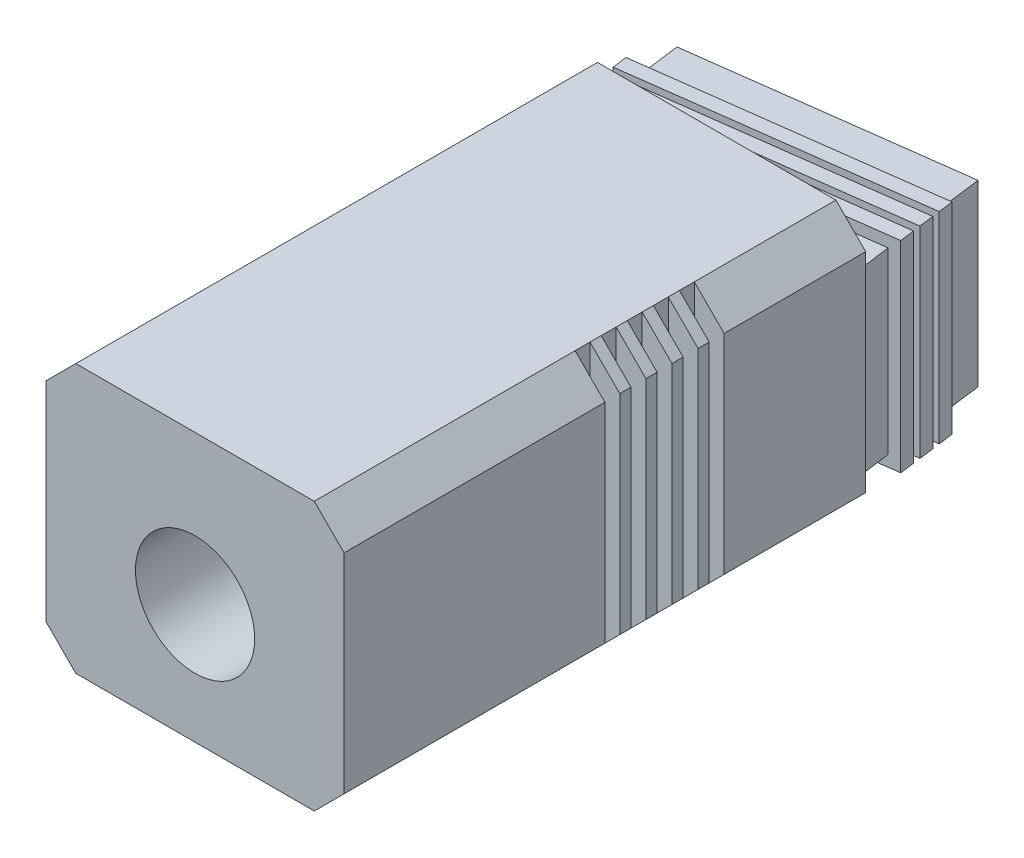
SolidWorks part; units mm, degrees
ref_plane "Front Plane" through (0, 0, 0) normal (0, 0, 1) x (1, 0, 0)
ref_plane "Top Plane" through (0, 0, 0) normal (0, 1, 0) x (1, 0, 0)
ref_plane "Right Plane" through (0, 0, 0) normal (1, 0, 0) x (0, 0, -1)
sketch "Sketch1" plane through (0, 0, 0) normal (0, 0, 1) x (1, 0, 0)
  line L0 (-10, 9) -> (-10, -9)
  line L1 (-10, 9) -> (10, 9)
  line L2 (-10, -9) -> (10, -9)
  line L3 (10, 9) -> (10, -9)
  line L4 (-10, 9) -> (10, -9) construction
  dimension "D1" = 20
  dimension "D2" = 18
extrude "Boss-Extrude1" add sketch "Sketch1" along normal blind 35
chamfer "Chamfer1" distance 2 angle 45 4 edges at (-10, 9, 17.5) (-10, -9, 17.5) (10, -9, 17.5) (10, 9, 17.5)
sketch "Sketch4" plane through (0, -9, 0) normal (0, -1, 0) x (1, 0, 0)
  line L0 (-8, 35) -> (-8, 0) construction
  line L1 (-8, 9.5) -> (-10, 9.5)
  line L2 (-8, 9.5) -> (-8, 10.5)
  line L3 (-8, 10.5) -> (-10, 10.5)
  line L4 (-10, 9.5) -> (-10, 10.5)
  line L5 (-10, 0) -> (-10, 35) construction
  line L6 (10, 17.5) -> (-8, 17.5) construction
  line L7 (-8, 11.25) -> (-10, 11.25)
  line L8 (-8, 11.25) -> (-8, 12.25)
  line L9 (-8, 12.25) -> (-10, 12.25)
  line L10 (-10, 11.25) -> (-10, 12.25)
  line L11 (-8, 13) -> (-10, 13)
  line L12 (-8, 13) -> (-8, 14)
  line L13 (-8, 14) -> (-10, 14)
  line L14 (-10, 13) -> (-10, 14)
  line L15 (-8, 14.75) -> (-10, 14.75)
  line L16 (-8, 14.75) -> (-8, 15.75)
  line L17 (-8, 15.75) -> (-10, 15.75)
  line L18 (-10, 14.75) -> (-10, 15.75)
  line L19 (-8, 16.5) -> (-10, 16.5)
  line L20 (-8, 16.5) -> (-8, 17.5)
  line L21 (-8, 17.5) -> (-10, 17.5)
  line L22 (-10, 16.5) -> (-10, 17.5)
  line L23 (10, 35) -> (10, 0) construction
  line L24 (0, 0) -> (0, 17.5) construction
  line L25 (10, 16.5) -> (10, 17.5)
  line L26 (8, 17.5) -> (10, 17.5)
  line L27 (8, 16.5) -> (8, 17.5)
  line L28 (8, 16.5) -> (10, 16.5)
  line L29 (10, 14.75) -> (10, 15.75)
  line L30 (8, 15.75) -> (10, 15.75)
  line L31 (8, 14.75) -> (8, 15.75)
  line L32 (8, 14.75) -> (10, 14.75)
  line L33 (10, 13) -> (10, 14)
  line L34 (8, 14) -> (10, 14)
  line L35 (8, 13) -> (8, 14)
  line L36 (8, 13) -> (10, 13)
  line L37 (10, 11.25) -> (10, 12.25)
  line L38 (8, 12.25) -> (10, 12.25)
  line L39 (8, 11.25) -> (8, 12.25)
  line L40 (8, 11.25) -> (10, 11.25)
  line L41 (10, 9.5) -> (10, 10.5)
  line L42 (8, 10.5) -> (10, 10.5)
  line L43 (8, 9.5) -> (8, 10.5)
  line L44 (8, 9.5) -> (10, 9.5)
  dimension "D2" = 1
  dimension "D4" = 0.75
  dimension "D3" = 5
extrude "Cut-Extrude2" cut sketch "Sketch4" against normal through all
sketch "Sketch7" plane through (0, -9, 0) normal (0, -1, 0) x (1, 0, 0)
  line L0 (-8.923, 2.3495) -> (8.923, 0)
  line L1 (-8.923, 2.3495) -> (-10.2283, -7.565)
  line L2 (8.923, 0) -> (7.6177, -9.9144)
  line L3 (-10.2283, -7.565) -> (7.6177, -9.9144)
  line L6 (-8, 0) -> (8, 0) construction
  line L7 (0, 0) -> (0, 1.1747) construction
  line L8 (8, 0) -> (10, 0) construction
  dimension "D1" = 7.5
  dimension "D2" = 18
  dimension "D3" = 10
extrude "Boss-Extrude3" add sketch "Sketch7" against normal blind 12 from offset 2 offset against normal yes
sketch "Sketch2" plane through (0, 0, 35) normal (0, 0, 1) x (1, 0, 0)
  line L0 (0, 0) -> (0, -1) construction
  circle A1 centre (0, -1) radius 4
  dimension "D1" = 1
  dimension "D3" = 8
extrude "Cut-Extrude1" cut sketch "Sketch2" against normal up to surface (35 mm away) up to face at (0, 0, 0)
sketch "Sketch8" plane through (-1.1532, 0, -8.7597) normal (-0.1305, 0, -0.9914) x (-0.9914, 0, 0.1305)
  line L0 (0, 0) -> (0, -1) construction
  circle A0 centre (0, -1) radius 4
  dimension "D1" = 8
  dimension "D2" = 1
sketch "Sketch9" plane through (0, 0, 0) normal (0, 0, 1) x (1, 0, 0)
  circle A0 centre (0, -1) radius 4
  circle A1 centre (0, -1) radius 4 construction
loft "Cut-Loft1" cut profiles "Sketch8", "Sketch9"
sketch "Sketch10" plane through (-1.1532, 0, -8.7597) normal (-0.1305, 0, -0.9914) x (-0.9914, 0, 0.1305)
  line L0 (0.1533, 5) -> (0.1533, 5.75) construction
  line L1 (-9.5967, 5.75) -> (9.9033, 5.75)
  line L2 (-9.5967, 5.75) -> (-9.5967, -7.75)
  line L3 (-9.5967, -7.75) -> (9.9033, -7.75)
  line L4 (9.9033, 5.75) -> (9.9033, -7.75)
  line L5 (-8.8467, 5) -> (9.1533, 5) construction
  line L6 (-8.8467, -1) -> (-9.5967, -1) construction
  line L7 (-8.8467, 5) -> (-8.8467, -7) construction
  circle A0 centre (0, -1) radius 5
  ellipse E0 centre (0, -1) end of major axis (0, -5) minor radius 3.9658 construction
  dimension "D2" = 10
  dimension "D1" = 0.75
extrude "Boss-Extrude4" add sketch "Sketch10" against normal blind 1 from offset 6 offset against normal yes
pattern_linear "LPattern1" count 3 spacing 1.5 along (-0.1305, 0, -0.9914) of "Boss-Extrude4"
sketch "Sketch11" plane through (0, -7, 0) normal (0, -1, 0) x (1, 0, 0)
  line L0 (-9.7062, -3.5992) -> (8.1398, -5.9487)
  line L1 (-9.7062, -3.5992) -> (-9.4451, -1.6163)
  line L2 (8.1398, -5.9487) -> (8.4009, -3.9658)
  line L3 (-9.4451, -1.6163) -> (8.4009, -3.9658)
extrude "Boss-Extrude5" add sketch "Sketch11" along normal up to surface (0.75 mm away) up to face at (-0.4568, -7.75, -2.2953)
